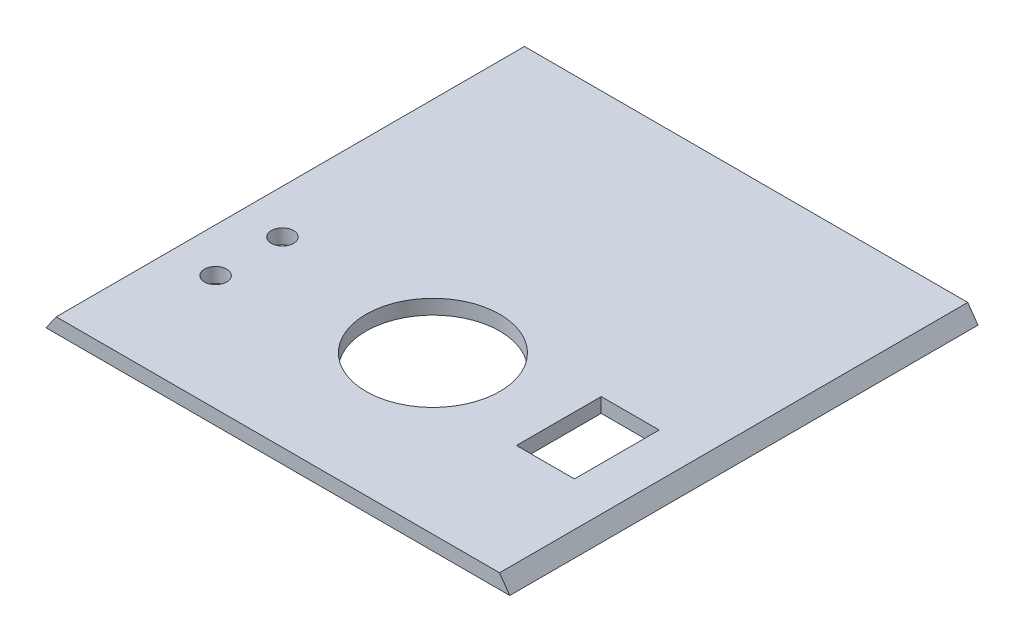
SolidWorks part; units mm, degrees
ref_plane "Front Plane" through (0, 0, 0) normal (0, 0, 1) x (1, 0, 0)
ref_plane "Top Plane" through (0, 0, 0) normal (0, 1, 0) x (1, 0, 0)
ref_plane "Right Plane" through (0, 0, 0) normal (1, 0, 0) x (0, 0, -1)
sketch "Sketch1" plane through (0, 0, 0) normal (0, 0, 1) x (1, 0, 0)
  line L0 (-48.1684, -4.9263) -> (55.8316, -4.9263)
  line L1 (-48.1684, -4.9263) -> (-45.8741, -1.6497)
  line L2 (55.8316, -4.9263) -> (53.5373, -1.6497)
  line L3 (-45.8741, -1.6497) -> (53.5373, -1.6497)
  dimension "D1" = 104
  dimension "D2" = 4
  dimension "D3" = 4
  dimension "D4" = 55
  dimension "D5" = 55
extrude "Boss-Extrude1" add sketch "Sketch1" against normal blind 105
sketch "Sketch2" plane through (0, -1.6497, 0) normal (0, 1, 0) x (1, 0, 0)
  circle A0 centre (3.3625, 35.2345) radius 15
extrude "Cut-Extrude1" cut sketch "Sketch2" against normal through all and the other way through all
sketch "Sketch3" plane through (0, -1.6497, 0) normal (0, 1, 0) x (1, 0, 0)
  circle A0 centre (-36.0169, 25.8752) radius 2.5
  circle A1 centre (-36.0169, 40.8752) radius 2.5
  dimension "D2" = 5
  dimension "D3" = 5
  dimension "D1" = 15
extrude "Cut-Extrude2" cut sketch "Sketch3" against normal up to next and the other way through all
sketch "Sketch4" plane through (0, -1.6497, 0) normal (0, 1, 0) x (1, 0, 0)
  line L1 (30.7148, 26.6194) -> (43.7148, 26.6194)
  line L2 (30.7148, 26.6194) -> (30.7148, 45.6194)
  line L3 (30.7148, 45.6194) -> (43.7148, 45.6194)
  line L4 (43.7148, 26.6194) -> (43.7148, 45.6194)
  dimension "D1" = 13
  dimension "D2" = 19
extrude "Cut-Extrude3" cut sketch "Sketch4" against normal up to next
